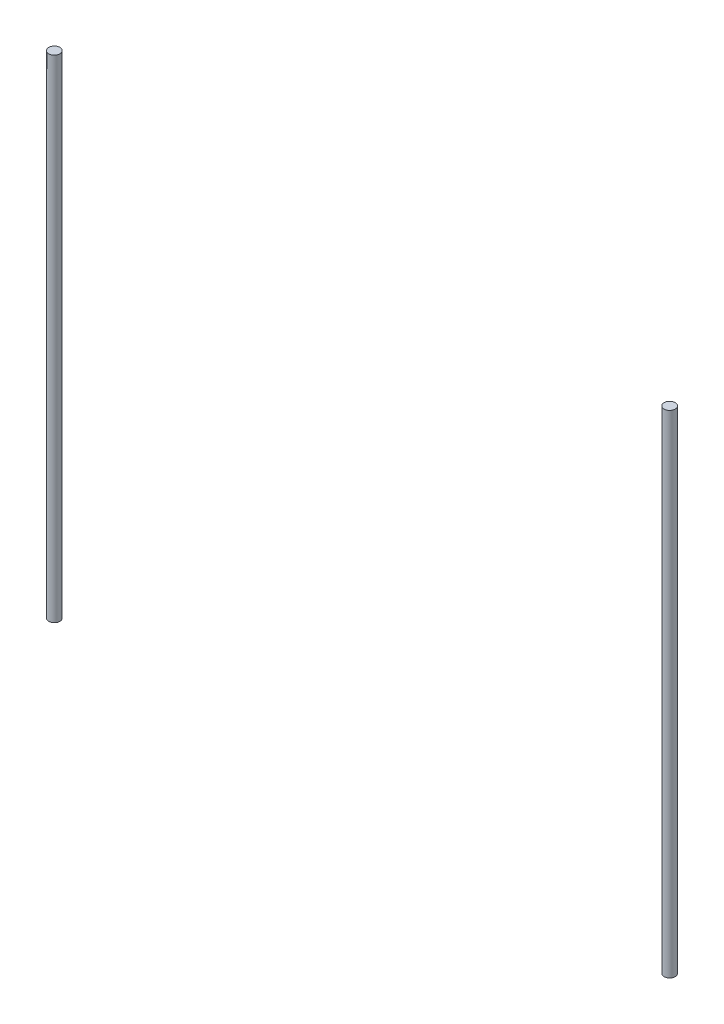
SolidWorks part; units mm, degrees
ref_plane "Front Plane" through (0, 0, 0) normal (0, 0, 1) x (1, 0, 0)
ref_plane "Top Plane" through (0, 0, 0) normal (0, 1, 0) x (1, 0, 0)
ref_plane "Right Plane" through (0, 0, 0) normal (1, 0, 0) x (0, 0, -1)
sketch "Sketch1" plane through (0, 0, 0) normal (0, 1, 0) x (1, 0, 0)
  circle A0 centre (-220, 0) radius 4
  circle A1 centre (220, 0) radius 4
extrude "Boss-Extrude1" add sketch "Sketch1" along normal blind 351.5 from offset 0
